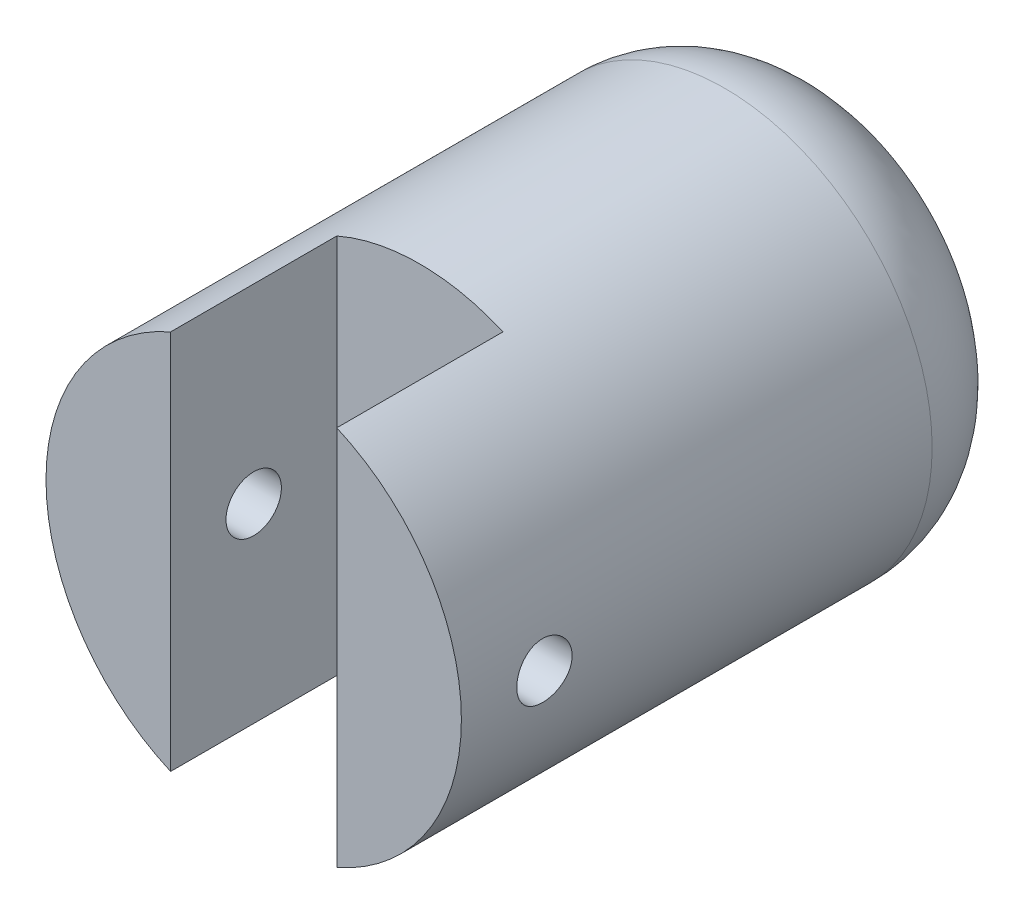
SolidWorks part; units mm, degrees
ref_plane "Alzado" through (0, 0, 0) normal (0, 0, 1) x (1, 0, 0)
ref_plane "Planta" through (0, 0, 0) normal (0, 1, 0) x (1, 0, 0)
ref_plane "Vista lateral" through (0, 0, 0) normal (1, 0, 0) x (0, 0, -1)
sketch "Croquis1" plane through (0, 0, 0) normal (0, 0, 1) x (1, 0, 0)
  circle A0 centre (0, 0) radius 7.5
  dimension "D1" = 15
extrude "Saliente-Extruir1" add sketch "Croquis1" along normal blind 21
sketch "Croquis2" plane through (0, 0, 0) normal (1, 0, 0) x (0, 0, -1)
  line L0 (-21, 0) -> (-18, 0) construction
  line L1 (-21, 7.5) -> (-21, -7.5) construction
  circle A0 centre (-18, 0) radius 1
  dimension "D2" = 2
  dimension "D1" = 3
extrude "Cortar-Extruir1" cut sketch "Croquis2" against normal mid plane 21
sketch "Croquis3" plane through (0, 0, 21) normal (0, 0, 1) x (1, 0, 0)
  line L0 (0, 7.5) -> (0, -7.5) construction
  line L2 (-3, -9) -> (3, -9)
  line L3 (-3, -9) -> (-3, 9)
  line L4 (-3, 9) -> (3, 9)
  line L5 (3, -9) -> (3, 9)
  line L6 (-3, -9) -> (3, 9) construction
  line L7 (-3, 9) -> (3, -9) construction
  circle A0 centre (0, 0) radius 7.5 construction
  point P5 (0, 0)
  dimension "D1" = 6
  dimension "D2" = 18
extrude "Cortar-Extruir2" cut sketch "Croquis3" against normal blind 6
fillet "Redondeo1" radius 4 1 edges at (7.5, 0, 0)
